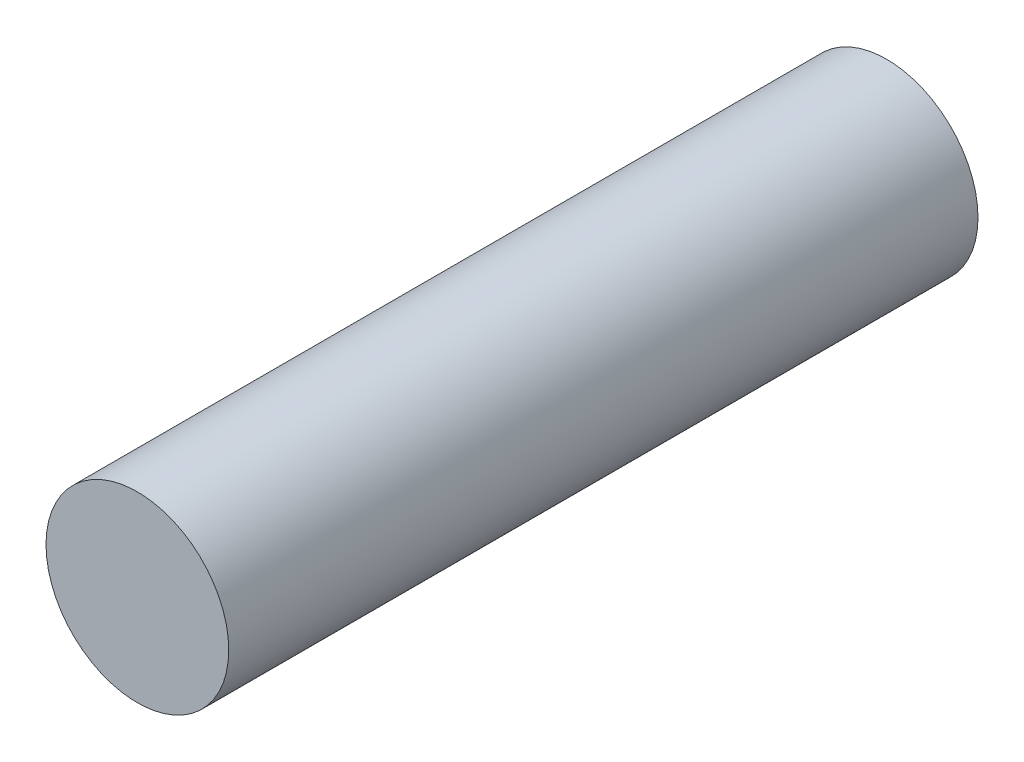
SolidWorks part; units mm, degrees
ref_plane "Front Plane" through (0, 0, 0) normal (0, 0, 1) x (1, 0, 0)
ref_plane "Top Plane" through (0, 0, 0) normal (0, 1, 0) x (1, 0, 0)
ref_plane "Right Plane" through (0, 0, 0) normal (1, 0, 0) x (0, 0, -1)
sketch "Sketch2" plane through (0, 0, 0) normal (0, 0, 1) x (1, 0, 0)
  circle A4 centre (0, 0) radius 2.5
  point P3 (25, 0)
  dimension "D1" = 5
ref_plane "Plane1" through (0, 0, 20.5) normal (0, 0, 1) x (1, 0, 0)
sketch "Sketch3" plane through (0, 0, 20.5) normal (0, 0, 1) x (1, 0, 0)
  circle A0 centre (0, 0) radius 2.5
  dimension "D1" = 5
loft "Loft1" add profiles "Sketch2", "Sketch3"
